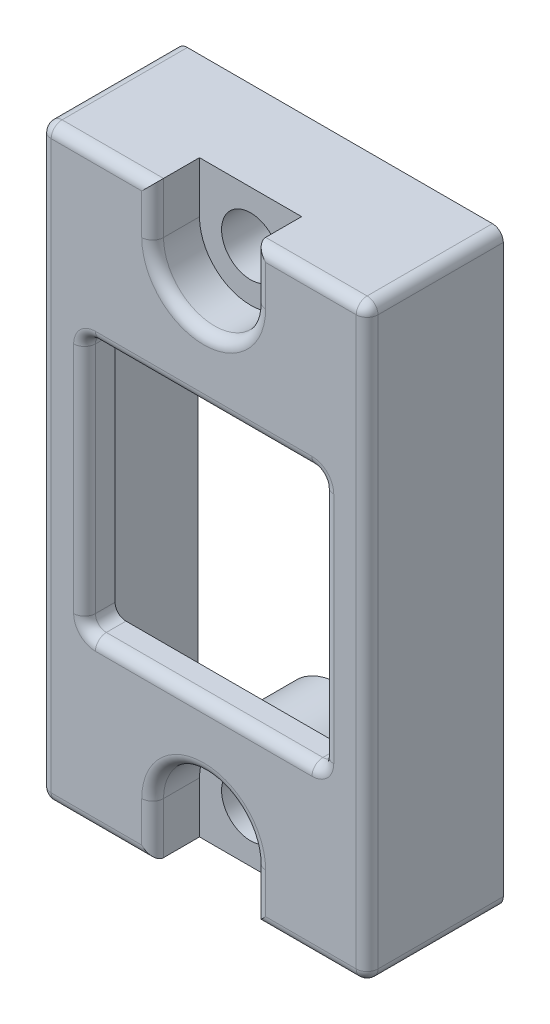
SolidWorks part; units mm, degrees
material "Nylon 101"
ref_plane "Front Plane" through (0, 0, 0) normal (0, 0, 1) x (1, 0, 0)
ref_plane "Top Plane" through (0, 0, 0) normal (0, 1, 0) x (1, 0, 0)
ref_plane "Right Plane" through (0, 0, 0) normal (1, 0, 0) x (0, 0, -1)
sketch "Sketch1" plane through (0, 0, 0) normal (0, 0, 1) x (1, 0, 0)
  line L0 (73.66, -84.3122) -> (66.04, -84.3122) construction
  line L2 (81.28, -96.5042) -> (81.28, -72.1202)
  line L3 (81.28, -96.5042) -> (81.28, -98.0282)
  line L4 (66.04, -96.5042) -> (66.04, -72.1202)
  line L5 (81.28, -96.5042) -> (66.04, -72.1202) construction
  line L6 (81.28, -72.1202) -> (66.04, -96.5042) construction
  line L7 (66.04, -96.5042) -> (66.04, -98.0282)
  line L8 (66.04, -72.1202) -> (66.04, -70.5962)
  line L9 (66.04, -70.5962) -> (81.28, -70.5962)
  line L10 (81.28, -72.1202) -> (81.28, -70.5962)
  line L11 (66.04, -72.1202) -> (81.28, -70.5962) construction
  line L12 (66.04, -70.5962) -> (81.28, -72.1202) construction
  line L13 (66.04, -98.0282) -> (81.28, -98.0282)
  point P4 (73.66, -84.3122)
  point P10 (73.66, -71.3582)
  dimension "D1" = 1.524
extrude "Boss-Extrude1" add sketch "Sketch1" along normal blind 6.35
sketch "Sketch2" plane through (0, 0, 6.35) normal (0, 0, 1) x (1, 0, 0)
  line L5 (68.1037, -78.3591) -> (68.1037, -90.2654)
  line L6 (79.2162, -78.3591) -> (68.1037, -78.3591)
  line L7 (79.2162, -90.2654) -> (79.2162, -78.3591)
  line L8 (68.1037, -90.2654) -> (79.2162, -90.2654)
  line L9 (68.1037, -78.3591) -> (68.1037, -90.2654)
  line L10 (79.2162, -78.3591) -> (68.1037, -78.3591)
  line L11 (79.2162, -90.2654) -> (79.2162, -78.3591)
  line L12 (68.1037, -90.2654) -> (79.2162, -90.2654)
  dimension "D1" = 0
extrude "Cut-Extrude1" cut sketch "Sketch2" against normal through all
shell "Shell1" thickness 1
sketch "Sketch5" plane through (0, 0, 0) normal (0, 0, -1) x (-1, 0, 0)
  line L0 (-73.66, -98.0282) -> (-73.66, -70.5962) construction
  line L1 (-66.04, -98.0282) -> (-81.28, -98.0282) construction
  line L2 (-81.28, -70.5962) -> (-66.04, -70.5962) construction
  line L3 (-70.7724, -76.3714) -> (-70.7724, -70.5962)
  line L4 (-81.28, -98.0282) -> (-81.28, -70.5962) construction
  line L5 (-81.28, -84.3122) -> (-73.66, -84.3122) construction
  line L6 (-76.5476, -92.253) -> (-70.7724, -92.253)
  line L7 (-76.5476, -92.253) -> (-76.5476, -98.0282)
  line L8 (-76.5476, -98.0282) -> (-70.7724, -98.0282)
  line L9 (-70.7724, -92.253) -> (-70.7724, -98.0282)
  line L10 (-76.5476, -92.253) -> (-70.7724, -98.0282) construction
  line L11 (-76.5476, -98.0282) -> (-70.7724, -92.253) construction
  line L12 (-76.5476, -76.3714) -> (-70.7724, -76.3714)
  line L13 (-76.5476, -76.3714) -> (-76.5476, -70.5962)
  line L14 (-76.5476, -70.5962) -> (-70.7724, -70.5962)
  point P6 (-73.66, -95.1406)
  dimension "D1" = 5.7752
extrude "Boss-Extrude2" add sketch "Sketch5" against normal through all
hole_wizard "CBORE for #2 Socket Head Cap Screw2" positions "Sketch4" profile "Sketch3" counterbore size "#2" standard "ANSI Inch" end condition through all
sketch "Sketch4" plane through (0, 0, 6.35) normal (0, 0, 1) x (1, 0, 0)
  line L0 (73.66, -70.5962) -> (73.66, -98.0282) construction
  line L1 (81.28, -70.5962) -> (66.04, -70.5962) construction
  line L2 (66.04, -98.0282) -> (81.28, -98.0282) construction
  line L3 (73.66, -84.3122) -> (81.28, -84.3122) construction
  line L4 (81.28, -98.0282) -> (81.28, -70.5962) construction
  point P0 (73.66, -95.6406)
  point P23 (73.66, -72.9838)
  dimension "D1" = 2.3876
sketch "Sketch3" plane through (73.66, -95.6406, 6.35) normal (1, 0, 0) x (0, -1, 0)
  line L0 (0, 0) -> (0, 6.35)
  line L1 (0, 6.35) -> (1.3525, 6.35)
  line L3 (1.3525, 6.35) -> (1.3525, 2.1844)
  line L4 (1.3525, 2.1844) -> (2.3812, 2.1844)
  line L5 (2.3812, 2.1844) -> (2.3812, 0)
  line L7 (2.3812, 0) -> (0, 0)
  line L11 (0, -6.35) -> (0, 107.95) construction
  dimension "Thru Hole Dia." = 2.7051
  dimension "Thru Hole Depth" = 6.35
  dimension "C'Bore Dia." = 4.7625
  dimension "C'Bore Depth" = 2.1844
sketch "Sketch6" plane through (0, 0, 0) normal (0, 0, -1) x (-1, 0, 0)
  line L0 (-76.5476, -92.253) -> (-76.5476, -97.0282) construction
  line L1 (-76.5476, -95.6406) -> (-76.8016, -95.6406)
  line L2 (-76.8016, -95.6406) -> (-76.8016, -92.253)
  line L3 (-76.8016, -92.253) -> (-70.5184, -92.253)
  line L4 (-70.7724, -92.253) -> (-76.5476, -92.253) construction
  line L5 (-73.66, -95.6406) -> (-73.66, -92.753) construction
  line L6 (-70.7724, -95.6406) -> (-70.5184, -95.6406)
  line L7 (-70.5184, -95.6406) -> (-70.5184, -92.253)
  line L8 (-79.2162, -84.3122) -> (-68.1037, -84.3122) construction
  line L9 (-79.2162, -90.2654) -> (-79.2162, -78.3591) construction
  line L10 (-68.1037, -78.3591) -> (-68.1037, -90.2654) construction
  line L11 (-76.8016, -72.9838) -> (-76.8016, -76.3714)
  line L12 (-76.5476, -72.9838) -> (-76.8016, -72.9838)
  line L13 (-70.7724, -72.9838) -> (-70.5184, -72.9838)
  line L14 (-70.5184, -72.9838) -> (-70.5184, -76.3714)
  line L15 (-76.8016, -76.3714) -> (-70.5184, -76.3714)
  arc A1 (-70.7724, -95.6406) -> (-76.5476, -95.6406) centre (-73.66, -95.6406) ccw
  arc A2 (-70.7724, -72.9838) -> (-76.5476, -72.9838) centre (-73.66, -72.9838) cw
  point P15 (-73.66, -92.253)
  dimension "D1" = 0.254
extrude "Cut-Extrude2" cut sketch "Sketch6" against normal offset from surface (4.9276 mm away) 1.4224 up to face at (76.0413, -95.6406, 6.35)
sketch "Sketch7" plane through (0, 0, 5.35) normal (0, 0, -1) x (-1, 0, 0)
  line L4 (-79.2162, -90.2654) -> (-68.1037, -90.2654)
  line L5 (-79.2162, -78.3591) -> (-79.2162, -90.2654)
  line L6 (-68.1037, -78.3591) -> (-79.2162, -78.3591)
  line L7 (-68.1037, -90.2654) -> (-68.1037, -78.3591)
  line L8 (-79.2162, -90.2654) -> (-68.1037, -90.2654)
  line L9 (-79.2162, -78.3591) -> (-79.2162, -90.2654)
  line L10 (-68.1037, -78.3591) -> (-79.2162, -78.3591)
  line L11 (-68.1037, -90.2654) -> (-68.1037, -78.3591)
  line L12 (-70.7724, -76.3714) -> (-76.5476, -76.3714)
  line L13 (-76.5476, -76.3714) -> (-76.5476, -71.5962)
  line L14 (-76.5476, -71.5962) -> (-80.28, -71.5962)
  line L15 (-80.28, -71.5962) -> (-80.28, -97.0282)
  line L16 (-80.28, -97.0282) -> (-76.5476, -97.0282)
  line L17 (-76.5476, -97.0282) -> (-76.5476, -92.253)
  line L18 (-76.5476, -92.253) -> (-70.7724, -92.253)
  line L19 (-70.7724, -92.253) -> (-70.7724, -97.0282)
  line L20 (-70.7724, -97.0282) -> (-67.04, -97.0282)
  line L21 (-67.04, -97.0282) -> (-67.04, -71.5962)
  line L22 (-67.04, -71.5962) -> (-70.7724, -71.5962)
  line L23 (-70.7724, -71.5962) -> (-70.7724, -76.3714)
  line L24 (-70.7724, -76.3714) -> (-76.5476, -76.3714)
  line L25 (-76.5476, -76.3714) -> (-76.5476, -71.5962)
  line L26 (-76.5476, -71.5962) -> (-80.28, -71.5962)
  line L27 (-80.28, -71.5962) -> (-80.28, -97.0282)
  line L28 (-80.28, -97.0282) -> (-76.5476, -97.0282)
  line L29 (-76.5476, -97.0282) -> (-76.5476, -92.253)
  line L30 (-76.5476, -92.253) -> (-70.7724, -92.253)
  line L31 (-70.7724, -92.253) -> (-70.7724, -97.0282)
  line L32 (-70.7724, -97.0282) -> (-67.04, -97.0282)
  line L33 (-67.04, -97.0282) -> (-67.04, -71.5962)
  line L34 (-67.04, -71.5962) -> (-70.7724, -71.5962)
  line L35 (-70.7724, -71.5962) -> (-70.7724, -76.3714)
  dimension "D1" = 0
  dimension "D2" = 0
extrude "Boss-Extrude4" add sketch "Sketch7" along normal up to surface (0.4224 mm away) up to face at (73.66, -75.3995, 4.9276)
sketch "Sketch8" plane through (0, 0, 6.35) normal (0, 0, 1) x (1, 0, 0)
  line L0 (66.04, -98.0282) -> (81.28, -98.0282) construction
  line L1 (71.2788, -95.6406) -> (76.0413, -95.6406)
  line L2 (71.2788, -95.6406) -> (71.2788, -98.0282)
  line L3 (71.2788, -98.0282) -> (76.0413, -98.0282)
  line L4 (76.0413, -95.6406) -> (76.0413, -98.0282)
  line L5 (71.2788, -95.6406) -> (76.0413, -98.0282) construction
  line L6 (71.2788, -98.0282) -> (76.0413, -95.6406) construction
  line L7 (68.1037, -84.3122) -> (79.2162, -84.3122) construction
  line L8 (68.1037, -78.3591) -> (68.1037, -90.2654) construction
  line L9 (79.2162, -90.2654) -> (79.2162, -78.3591) construction
  line L10 (71.2788, -72.9838) -> (71.2788, -70.5962)
  line L11 (71.2788, -70.5962) -> (76.0413, -70.5962)
  line L12 (76.0413, -72.9838) -> (76.0413, -70.5962)
  line L13 (71.2788, -72.9838) -> (76.0413, -72.9838)
  circle A0 centre (73.66, -95.6406) radius 2.3813 construction
  point P4 (73.66, -96.8344)
  point P7 (73.66, -95.6406)
extrude "Cut-Extrude3" cut sketch "Sketch8" against normal up to surface (2.1844 mm away) up to face at (75.0125, -95.6406, 4.1656)
fillet "Fillet1" radius 0.508 24 edges at (79.2162, -84.3122, 6.35) (73.66, -78.3591, 6.35) (68.1037, -84.3122, 6.35) (73.66, -90.2654, 6.35) (78.6606, -70.5962, 6.35) (81.28, -84.3122, 6.35) (78.6606, -98.0282, 6.35) (76.0413, -96.8344, 6.35) (73.66, -93.2594, 6.35) (71.2788, -96.8344, 6.35) (68.6594, -98.0282, 6.35) (66.04, -84.3122, 6.35) (68.6594, -70.5962, 6.35) (71.2788, -71.79, 6.35) (73.66, -75.3651, 6.35) (76.0413, -71.79, 6.35) (66.04, -98.0282, 3.175) (66.04, -70.5962, 3.175) (81.28, -70.5962, 3.175) (81.28, -98.0282, 3.175) (68.1037, -78.3591, 5.6388) (79.2162, -78.3591, 5.6388) (79.2162, -90.2654, 5.6388) (68.1037, -90.2654, 5.6388)
